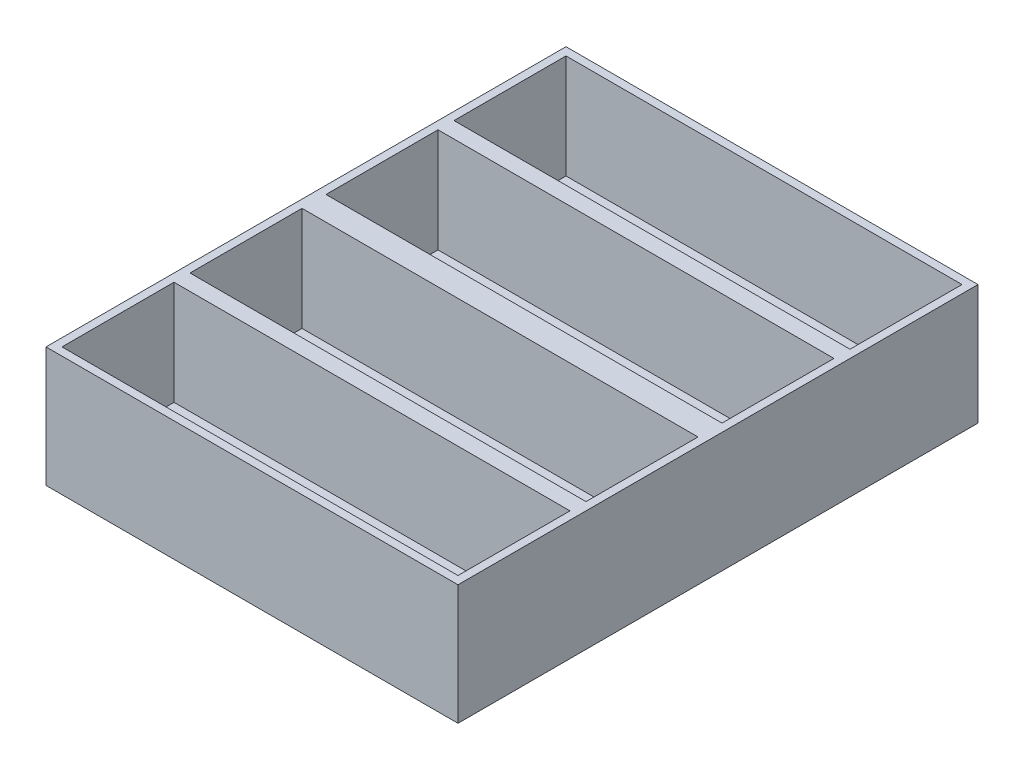
SolidWorks part; units mm, degrees
material "ABS"
ref_plane "Front Plane" through (0, 0, 0) normal (0, 0, 1) x (1, 0, 0)
ref_plane "Top Plane" through (0, 0, 0) normal (0, 1, 0) x (1, 0, 0)
ref_plane "Right Plane" through (0, 0, 0) normal (1, 0, 0) x (0, 0, -1)
ref_plane "Top Plane1" through (0, 15, 0) normal (0, 1, 0) x (1, 0, 0)
sketch "Sketch1" plane through (0, 0, 0) normal (0, 1, 0) x (1, 0, 0)
  line L0 (-25.75, 32.5) -> (25.75, -32.5) construction
  line L1 (-25.75, 32.5) -> (25.75, 32.5)
  line L2 (-25.75, 32.5) -> (-25.75, -32.5)
  line L3 (-25.75, -32.5) -> (25.75, -32.5)
  line L4 (25.75, 32.5) -> (25.75, -32.5)
  circle A0 centre (-7.5, -13) radius 1.5025
  circle A1 centre (7.5, -13) radius 1.5025
  circle A2 centre (7.5, 22) radius 1.5025
  circle A3 centre (-7.5, 22) radius 1.5025
  dimension "D3" = 3.005
  dimension "D4" = 15
  dimension "D5" = 15
  dimension "D6" = 10.5
  dimension "D7" = 19.5
  dimension "D8" = 18.25
  dimension "D9" = 19.5
  dimension "D10" = 10.5
  dimension "D11" = 18.25
  dimension "D1" = 51.5
  dimension "D2" = 65
extrude "Boss-Extrude1" add sketch "Sketch1" along normal blind 15
sketch "Sketch2" plane through (0, 15, 0) normal (0, 1, 0) x (1, 0, 0)
  line L0 (-25.75, 0) -> (25.75, 0) construction
  line L1 (-25.75, 32.5) -> (-25.75, -32.5) construction
  line L2 (25.75, -32.5) -> (25.75, 32.5) construction
  line L3 (-25.75, -32.5) -> (25.75, -32.5) construction
  line L4 (-24.75, -1.5) -> (24.75, -1.5)
  line L5 (-24.75, -1.5) -> (-24.75, -15.5)
  line L6 (-24.75, -31.5) -> (24.75, -31.5)
  line L7 (24.75, -1.5) -> (24.75, -15.5)
  line L8 (-24.75, -17.5) -> (24.75, -17.5)
  line L9 (-24.75, -15.5) -> (24.75, -15.5)
  line L10 (-24.75, -17.5) -> (-24.75, -31.5)
  line L11 (24.75, -17.5) -> (24.75, -31.5)
  line L12 (24.75, 17.5) -> (24.75, 31.5)
  line L13 (-24.75, 17.5) -> (-24.75, 31.5)
  line L14 (-24.75, 15.5) -> (24.75, 15.5)
  line L15 (-24.75, 17.5) -> (24.75, 17.5)
  line L16 (24.75, 1.5) -> (24.75, 15.5)
  line L17 (-24.75, 31.5) -> (24.75, 31.5)
  line L18 (-24.75, 1.5) -> (-24.75, 15.5)
  line L19 (-24.75, 1.5) -> (24.75, 1.5)
  dimension "D1" = 1
  dimension "D2" = 1.5
  dimension "D3" = 1
  dimension "D4" = 1
  dimension "D5" = 2
  dimension "D6" = 14
extrude "Cut-Extrude1" cut sketch "Sketch2" along direction (0, 1, 0) on the side against the normal blind 13
